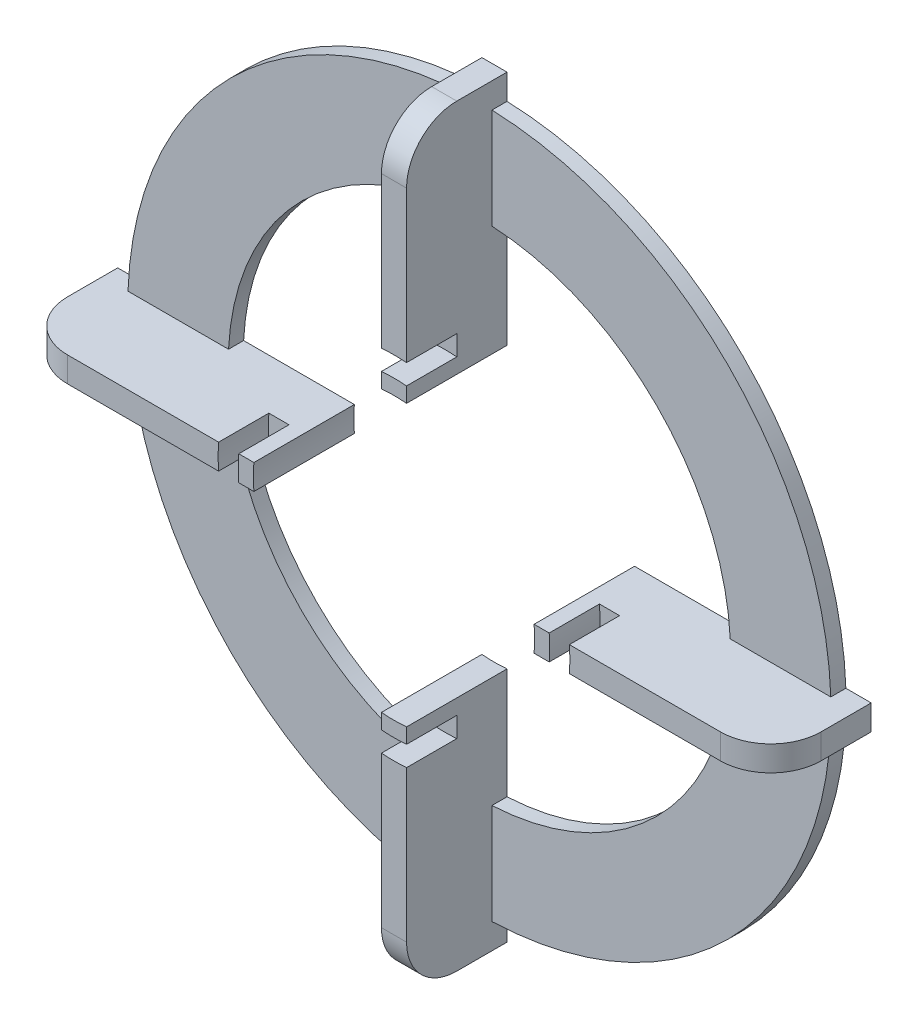
SolidWorks part; units mm, degrees
ref_plane "Front Plane" through (0, 0, 0) normal (0, 0, 1) x (1, 0, 0)
ref_plane "Top Plane" through (0, 0, 0) normal (0, 1, 0) x (1, 0, 0)
ref_plane "Right Plane" through (0, 0, 0) normal (1, 0, 0) x (0, 0, -1)
sketch "Sketch1" plane through (0, 0, 0) normal (0, 0, 1) x (1, 0, 0)
  line L1 (-2.5, 75) -> (2.5, 75)
  line L2 (-2.5, 75) -> (-2.5, -75)
  line L3 (-2.5, -75) -> (2.5, -75)
  line L4 (2.5, 75) -> (2.5, -75)
  line L5 (-2.5, 75) -> (2.5, -75) construction
  line L6 (-2.5, -75) -> (2.5, 75) construction
  line L7 (-75, 2.5) -> (75, 2.5)
  line L8 (-75, 2.5) -> (-75, -2.5)
  line L9 (-75, -2.5) -> (75, -2.5)
  line L10 (75, 2.5) -> (75, -2.5)
  line L11 (-75, 2.5) -> (75, -2.5) construction
  line L12 (-75, -2.5) -> (75, 2.5) construction
  point P0 (0, 0)
  point P6 (0, 0)
extrude "Boss-Extrude1" add sketch "Sketch1" along normal blind 20 contours L8 L9 L2 L7 | L10 L7 L4 L9 | L2 L7 L4 L1 | L9 L2 L3 L4 | L2 L9 L4 L7
sketch "Sketch2" plane through (0, 0, 0) normal (0, 0, -1) x (-1, 0, 0)
  circle A0 centre (0, 0) radius 50
  circle A1 centre (0, 0) radius 70
extrude "Boss-Extrude2" add sketch "Sketch2" against normal blind 3
sketch "Sketch3" plane through (0, 0, 20) normal (0, 0, 1) x (1, 0, 0)
  circle A0 centre (0, 0) radius 35
  circle A1 centre (0, 0) radius 31
extrude "Cut-Extrude1" cut sketch "Sketch3" against normal blind 10
sketch "Sketch4" plane through (0, 0, 20) normal (0, 0, 1) x (1, 0, 0)
  circle A0 centre (0, 0) radius 28
extrude "Cut-Extrude2" cut sketch "Sketch4" against normal through all
fillet "Fillet1" radius 10 1 edges at (0, 75, 20)
fillet "Fillet2" radius 10 1 edges at (75, 0, 20)
fillet "Fillet3" radius 10 1 edges at (-75, 0, 20)
fillet "Fillet4" radius 10 1 edges at (0, -75, 20)
